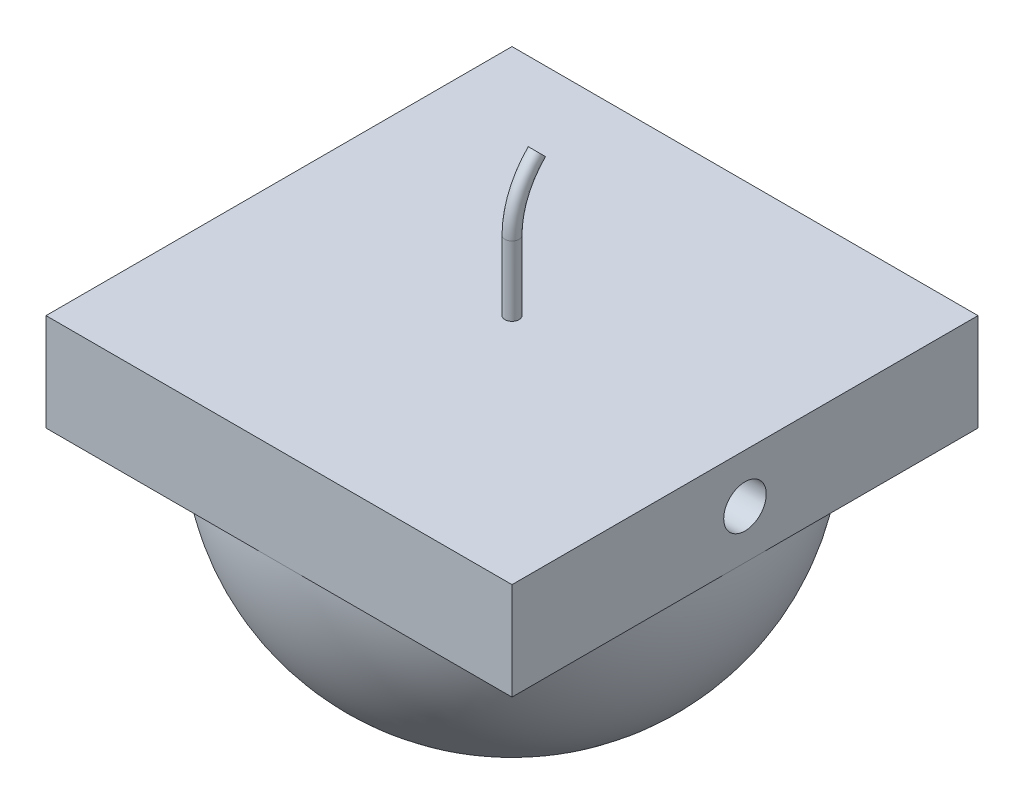
SolidWorks part; units mm, degrees
ref_plane "Front" through (0, 0, 0) normal (0, 0, 1) x (1, 0, 0)
ref_plane "Top" through (0, 0, 0) normal (0, 1, 0) x (1, 0, 0)
ref_plane "Right" through (0, 0, 0) normal (1, 0, 0) x (0, 0, -1)
sketch "Sketch1" plane through (0, 0, 0) normal (0, 1, 0) x (1, 0, 0)
  line L1 (-165.1, -165.1) -> (165.1, -165.1)
  line L2 (-165.1, -165.1) -> (-165.1, 165.1)
  line L3 (-165.1, 165.1) -> (165.1, 165.1)
  line L4 (165.1, -165.1) -> (165.1, 165.1)
  line L5 (-165.1, -165.1) -> (165.1, 165.1) construction
  line L6 (-165.1, 165.1) -> (165.1, -165.1) construction
  point P0 (0, 0)
  dimension "D2" = 330.2
extrude "Boss-Extrude1" add sketch "Sketch1" along normal blind 69.02
sketch "Sketch3" plane through (0, 0, 0) normal (-1, 0, 0) x (0, 0, 1)
  line L0 (-165.1, 0) -> (165.1, 69.02) construction
  circle A0 centre (0, 34.51) radius 15.0816
  point P2 (-58.3674, 44.7842)
  point P7 (0, 34.51)
  dimension "D1" = 30.1633
extrude "Cut-Extrude1" cut sketch "Sketch3" against normal through all both and the other way through all
sketch "Sketch4" plane through (0, 0, 0) normal (0, 1, 0) x (1, 0, 0)
  line L0 (165.1, -165.1) -> (-165.1, 165.1) construction
  line L1 (165.1, -165.1) -> (165.1, 165.1) construction
  line L2 (-116.7433, 116.7433) -> (116.7433, -116.7433)
  arc A0 (-116.7433, 116.7433) -> (116.7433, -116.7433) centre (0, 0) ccw
  arc A1 (116.7433, -116.7433) -> (-116.7433, 116.7433) centre (0, 0) ccw construction
revolve "Revolve3" add sketch "Sketch4" angle 180 about L0
sketch "Sketch5" plane through (0, 0, 0) normal (1, 0, 0) x (0, 0, -1)
  line L0 (0, 69.02) -> (0, 118.3078)
  line L1 (-165.1, 69.02) -> (165.1, 69.02) construction
  line L2 (0, 118.3078) -> (60.1561, 118.3078) construction
  line L3 (60.1561, 118.3078) -> (17.6193, 160.8446) construction
  arc A0 (17.6193, 160.8446) -> (0, 118.3078) centre (60.1561, 118.3078) ccw
  point P7 (60.3558, 118.3078)
  point P8 (100.0991, 163.2891)
  dimension "D1" = 118.3078
  dimension "D2" = 60.1561
  dimension "D3" = 45
sweep "Sweep1" add path "Sketch5" circular profile diameter 10 parameters "D3"=10
